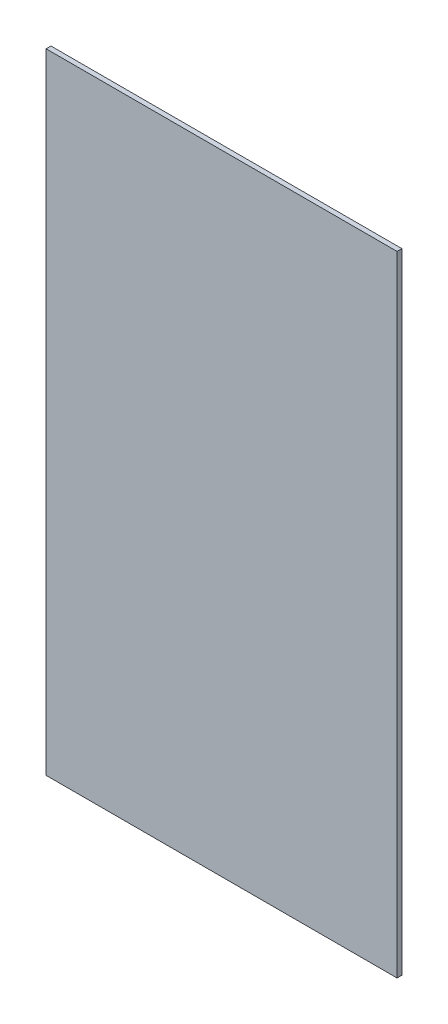
SolidWorks part; units mm, degrees
material "ABS PC"
ref_plane "Front Plane" through (0, 0, 0) normal (0, 0, 1) x (1, 0, 0)
ref_plane "Top Plane" through (0, 0, 0) normal (0, 1, 0) x (1, 0, 0)
ref_plane "Right Plane" through (0, 0, 0) normal (1, 0, 0) x (0, 0, -1)
sketch "Sketch1" plane through (0, 0, 0) normal (0, 0, 1) x (1, 0, 0)
  line L4 (-19.2734, 33.6237) -> (-10.0659, 33.6237)
  line L5 (-10.0659, 33.6237) -> (-10.0659, 50.1337)
  line L6 (-10.0659, 50.1337) -> (-19.2734, 50.1337)
  line L7 (-19.2734, 50.1337) -> (-19.2734, 33.6237)
  line L8 (-19.2734, 33.6237) -> (-10.0659, 33.6237)
  line L9 (-10.0659, 33.6237) -> (-10.0659, 50.1337)
  line L10 (-10.0659, 50.1337) -> (-19.2734, 50.1337)
  line L11 (-19.2734, 50.1337) -> (-19.2734, 33.6237)
  dimension "D1" = 0
extrude "Boss-Extrude1" add sketch "Sketch1" along normal blind 0.127
